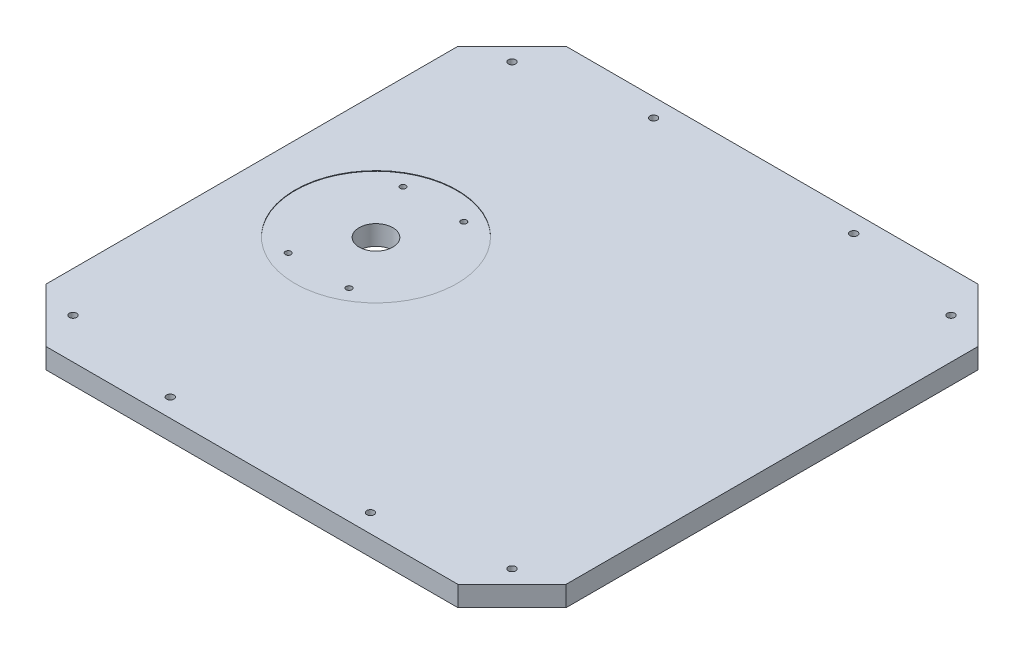
SolidWorks part; units mm, degrees
material "Al 6061-T6"
ref_plane "Front Plane" through (0, 0, 0) normal (0, 0, 1) x (1, 0, 0)
ref_plane "Top Plane" through (0, 0, 0) normal (0, 1, 0) x (1, 0, 0)
ref_plane "Right Plane" through (0, 0, 0) normal (1, 0, 0) x (0, 0, -1)
sketch "Sketch1" plane through (0, 0, 0) normal (0, 1, 0) x (1, 0, 0)
  line L0 (-96.8375, 122.2375) -> (-122.2375, 96.8375)
  line L1 (96.8375, -122.2375) -> (-96.8375, -122.2375)
  line L2 (122.2375, -96.8375) -> (122.2375, 96.8375)
  line L3 (96.8375, 122.2375) -> (-96.8375, 122.2375)
  line L4 (-122.2375, -96.8375) -> (-122.2375, 96.8375)
  line L5 (122.2375, -122.2375) -> (-122.2375, 122.2375) construction
  line L6 (122.2375, 122.2375) -> (-122.2375, -122.2375) construction
  line L7 (122.2375, 96.8375) -> (96.8375, 122.2375)
  line L8 (122.2375, -96.8375) -> (96.8375, -122.2375)
  line L9 (-96.8375, -122.2375) -> (-122.2375, -96.8375)
  point P0 (0, 0)
  dimension "D1" = 244.475
  dimension "D2" = 244.475
extrude "Boss-Extrude1" add sketch "Sketch1" along normal blind 9.525
hole_wizard "#8-32 Tapped Hole1" positions "Sketch2" profile "Sketch3" tap size "#8-32" standard "ANSI Inch" end condition through all
sketch "Sketch2" plane through (0, 9.525, 0) normal (0, 1, 0) x (1, 0, 0)
  line L0 (-122.2375, 96.8375) -> (-122.2375, -96.8375) construction
  line L1 (96.8375, 122.2375) -> (-96.8375, 122.2375) construction
  point P0 (-47.0535, 113.6015)
  point P14 (47.0535, 113.6015)
  point P15 (47.0535, -113.6015)
  point P16 (-47.0535, -113.6015)
  dimension "D1" = 75.184
  dimension "D2" = 8.636
  dimension "D3" = 2
  dimension "D4" = 2
sketch "Sketch3" plane through (-47.0535, 9.525, -113.6015) normal (1, 0, 0) x (0, 0, 1)
  line L0 (0, 0) -> (0, 9.525)
  line L1 (0, 9.525) -> (1.7272, 9.525)
  line L2 (1.7272, 9.525) -> (1.7272, 0)
  line L5 (1.7272, 0) -> (0, 0)
  line L11 (0, -6.35) -> (0, 107.95) construction
  dimension "Thru Tap Drill Dia." = 3.4544
  dimension "Thru Tap Drill Depth" = 9.525
cosmetic thread "Hole Thread1" parameters "D2"=4.1656
cosmetic thread "Hole Thread2" parameters "D2"=4.1656
cosmetic thread "Hole Thread3" parameters "D2"=4.1656
cosmetic thread "Hole Thread4" parameters "D2"=4.1656
hole_wizard "5/8 (0.625) Diameter Hole1" positions "Sketch4" profile "Sketch5" hole size "5/8" standard "ANSI Inch" end condition through all
sketch "Sketch4" plane through (0, 9.525, 0) normal (0, 1, 0) x (1, 0, 0)
  line L1 (122.2375, -96.8375) -> (122.2375, 96.8375) construction
  line L2 (96.8375, 122.2375) -> (-96.8375, 122.2375) construction
  point P0 (-63.9445, 0)
  point P8 (0, 0)
  point P9 (-63.9445, -18.9208)
  dimension "D1" = 186.182
  dimension "D2" = 122.2375
sketch "Sketch5" plane through (-63.9445, 9.525, 0) normal (1, 0, 0) x (0, 0, 1)
  line L0 (0, 0) -> (0, 9.525)
  line L1 (0, 9.525) -> (7.9375, 9.525)
  line L2 (7.9375, 9.525) -> (7.9375, 0)
  line L5 (7.9375, 0) -> (0, 0)
  line L11 (0, -6.35) -> (0, 107.95) construction
  dimension "Thru Hole Dia." = 15.875
  dimension "Thru Hole Depth" = 9.525
hole_wizard "#6-32 Tapped Hole1" positions "Sketch6" profile "Sketch7" tap size "#6-32" standard "ANSI Inch"
sketch "Sketch6" plane through (0, 9.525, 0) normal (0, 1, 0) x (1, 0, 0)
  circle A0 centre (-63.9445, 0) radius 7.9375 construction
  point P0 (-78.232, -26.9875)
  point P9 (-49.657, -26.9875)
  point P10 (-49.657, 26.9875)
  point P11 (-78.232, 26.9875)
  dimension "D1" = 26.9875
  dimension "D2" = 14.2875
  dimension "D3" = 2
  dimension "D4" = 2
sketch "Sketch7" plane through (-78.232, 9.525, 26.9875) normal (1, 0, 0) x (0, 0, 1)
  line L0 (0, 0) -> (0, 8.9407)
  line L1 (0, 8.9407) -> (1.3525, 8.128)
  line L2 (1.3525, 8.128) -> (1.3525, 0)
  line L5 (1.3525, 0) -> (0, 0)
  line L10 (0, 8.9407) -> (-1.3526, 8.128) construction
  line L11 (0, -6.35) -> (0, 107.95) construction
  dimension "Tap Drill Dia." = 2.7051
  dimension "Tap Drill Depth" = 8.128
  dimension "Drill Angle" = 118
cosmetic thread "Hole Thread5" parameters "D1"=6.35, "D2"=3.5052
cosmetic thread "Hole Thread6" parameters "D1"=6.35, "D2"=3.5052
cosmetic thread "Hole Thread7" parameters "D1"=6.35, "D2"=3.5052
cosmetic thread "Hole Thread8" parameters "D1"=6.35, "D2"=3.5052
sketch "Sketch8" plane through (0, 9.525, 0) normal (0, 1, 0) x (1, 0, 0)
  line L8 (96.8375, 122.2375) -> (-96.8375, 122.2375)
  line L9 (-96.8375, 122.2375) -> (-122.2375, 96.8375)
  line L10 (-122.2375, 96.8375) -> (-122.2375, -96.8375)
  line L11 (-122.2375, -96.8375) -> (-96.8375, -122.2375)
  line L12 (-96.8375, -122.2375) -> (96.8375, -122.2375)
  line L13 (96.8375, -122.2375) -> (122.2375, -96.8375)
  line L14 (122.2375, -96.8375) -> (122.2375, 96.8375)
  line L15 (122.2375, 96.8375) -> (96.8375, 122.2375)
  line L16 (96.8375, 122.2375) -> (-96.8375, 122.2375)
  line L17 (-96.8375, 122.2375) -> (-122.2375, 96.8375)
  line L18 (-122.2375, 96.8375) -> (-122.2375, -96.8375)
  line L19 (-122.2375, -96.8375) -> (-96.8375, -122.2375)
  line L20 (-96.8375, -122.2375) -> (96.8375, -122.2375)
  line L21 (96.8375, -122.2375) -> (122.2375, -96.8375)
  line L22 (122.2375, -96.8375) -> (122.2375, 96.8375)
  line L23 (122.2375, 96.8375) -> (96.8375, 122.2375)
  circle A0 centre (-63.9445, 0) radius 7.9375 construction
  circle A1 centre (-63.9445, 0) radius 7.9375
  circle A2 centre (-63.9445, 0) radius 38.1
  circle M9 centre (-78.232, -26.9875) radius 1.3525
  circle M10 centre (-49.657, -26.9875) radius 1.3525
  circle M11 centre (-49.657, 26.9875) radius 1.3525
  circle M12 centre (-78.232, 26.9875) radius 1.3525
  circle M25 centre (-63.9445, 0) radius 7.9375
  dimension "D2" = 76.2
  dimension "D1" = 0
extrude "Cut-Extrude1" cut sketch "Sketch8" against normal blind 0.254 contours A2 M9 M11 M25 M12 M10
hole_wizard "#8-32 Tapped Hole2" positions "Sketch10" profile "Sketch11" tap size "#8-32" standard "ANSI Inch" end condition through all
sketch "Sketch10" plane through (0, 9.525, 0) normal (0, 1, 0) x (1, 0, 0)
  line L0 (-122.2375, 96.8375) -> (-122.2375, -96.8375) construction
  line L1 (96.8375, 122.2375) -> (-96.8375, 122.2375) construction
  point P0 (-103.1875, 103.1875)
  point P11 (103.1875, 103.1875)
  point P12 (103.1875, -103.1875)
  point P13 (-103.1875, -103.1875)
  dimension "D1" = 19.05
  dimension "D2" = 19.05
  dimension "D3" = 2
  dimension "D4" = 2
sketch "Sketch11" plane through (-103.1875, 9.525, -103.1875) normal (1, 0, 0) x (0, 0, 1)
  line L0 (0, 0) -> (0, 9.525)
  line L1 (0, 9.525) -> (1.7272, 9.525)
  line L2 (1.7272, 9.525) -> (1.7272, 0)
  line L5 (1.7272, 0) -> (0, 0)
  line L11 (0, -6.35) -> (0, 107.95) construction
  dimension "Thru Tap Drill Dia." = 3.4544
  dimension "Thru Tap Drill Depth" = 9.525
cosmetic thread "Hole Thread9" parameters "D2"=4.1656
cosmetic thread "Hole Thread10" parameters "D2"=4.1656
cosmetic thread "Hole Thread11" parameters "D2"=4.1656
cosmetic thread "Hole Thread12" parameters "D2"=4.1656
hole_wizard "5/16 (0.3125) Diameter Hole1" positions "Sketch13" profile "Sketch14" hole size "5/16" standard "ANSI Inch"
sketch "Sketch13" plane through (0, 0, 0) normal (0, -1, 0) x (-1, 0, 0)
  line L0 (96.8375, -122.2375) -> (-96.8375, -122.2375) construction
  line L1 (-122.2375, -96.8375) -> (-122.2375, 96.8375) construction
  line L2 (122.2375, 96.8375) -> (122.2375, -96.8375) construction
  line L3 (-96.8375, 122.2375) -> (96.8375, 122.2375) construction
  line L4 (96.8375, -122.2375) -> (-96.8375, -122.2375)
  line L5 (-122.2375, -96.8375) -> (-122.2375, 96.8375)
  line L6 (122.2375, 96.8375) -> (122.2375, -96.8375)
  line L7 (-96.8375, 122.2375) -> (96.8375, 122.2375)
  circle A0 centre (63.9445, 0) radius 7.9375 construction
  circle A1 centre (63.9445, 0) radius 7.9375
  point P0 (85.0011, 0)
  point P2 (-85.0011, -52.5145)
  point P4 (-85.0011, 52.4891)
  point P9 (0, 0)
  point P18 (0, 0)
  dimension "D1" = 207.2386
  dimension "D2" = 37.2364
  dimension "D3" = 122.2375
  dimension "D4" = 69.7484
  dimension "D5" = 174.752
sketch "Sketch14" plane through (-85.0011, 0, 0) normal (1, 0, 0) x (0, 0, -1)
  line L0 (0, 0) -> (0, 7.4647)
  line L1 (0, 7.4647) -> (3.9687, 5.08)
  line L2 (3.9687, 5.08) -> (3.9687, 0)
  line L5 (3.9687, 0) -> (0, 0)
  line L10 (0, 7.4647) -> (-3.9688, 5.08) construction
  line L11 (0, -6.35) -> (0, 107.95) construction
  dimension "Hole Dia." = 7.9375
  dimension "Hole Depth" = 5.08
  dimension "Drill Angle" = 118
